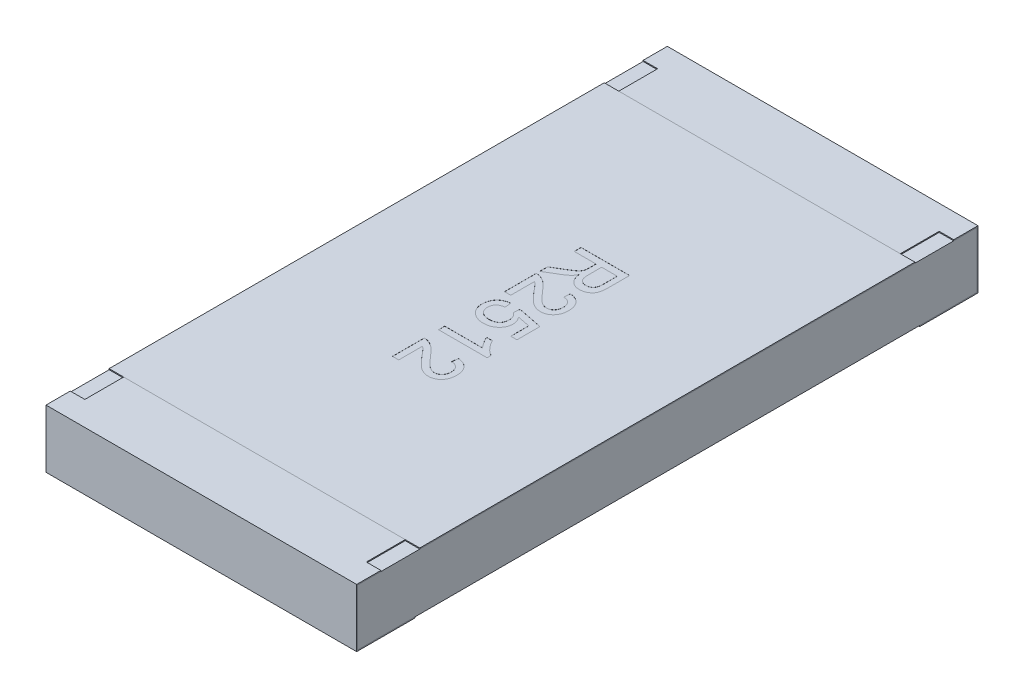
SolidWorks part; units mm, degrees
ref_plane "Front Plane" through (0, 0, 0) normal (0, 0, 1) x (1, 0, 0)
ref_plane "Top Plane" through (0, 0, 0) normal (0, 1, 0) x (1, 0, 0)
ref_plane "Right Plane" through (0, 0, 0) normal (1, 0, 0) x (0, 0, -1)
sketch "Sketch4" plane through (0, 0, 0) normal (1, 0, 0) x (0, 0, -1)
  line L0 (0, 0.1169) -> (0, -0.0721) construction
  line L1 (-3.2, 0) -> (0.3788, 0) construction
  line L2 (-3.2, 0.3) -> (-3.2, -0.3)
  line L3 (-3.2, -0.3) -> (-2.6, -0.3)
  line L4 (-2.55, 0.3) -> (-2.55, 0.29)
  line L5 (-2.55, 0.29) -> (-3.19, 0.29)
  line L6 (-3.19, 0.29) -> (-3.19, -0.29)
  line L7 (-3.19, -0.29) -> (-2.6, -0.29)
  line L8 (-2.6, -0.29) -> (-2.6, -0.3)
  line L9 (-2.55, 0.3) -> (-3.2, 0.3)
  line L10 (2.55, 0.3) -> (3.2, 0.3)
  line L11 (2.6, -0.29) -> (2.6, -0.3)
  line L12 (3.19, -0.29) -> (2.6, -0.29)
  line L13 (3.19, 0.29) -> (3.19, -0.29)
  line L14 (2.55, 0.29) -> (3.19, 0.29)
  line L15 (2.55, 0.3) -> (2.55, 0.29)
  line L16 (3.2, -0.3) -> (2.6, -0.3)
  line L17 (3.2, 0.3) -> (3.2, -0.3)
  dimension "LENGTH" = 3.2
  dimension "HEIGHT" = 0.6
  dimension "END CAP TOP LENGTH" = 0.65
  dimension "END CAP BOTTOM LENGTH" = 0.6
  dimension "D5" = 0.01
  dimension "D6" = 0.01
extrude "Boss-Extrude2" add sketch "Sketch4" along normal mid plane 3.2
sketch "Sketch5" plane through (0, 0, 0) normal (1, 0, 0) x (0, 0, -1)
  line L1 (-3.19, 0.29) -> (3.19, 0.29)
  line L2 (-3.19, 0.29) -> (-3.19, -0.29)
  line L3 (-3.19, -0.29) -> (3.19, -0.29)
  line L4 (3.19, 0.29) -> (3.19, -0.29)
extrude "Boss-Extrude3" add sketch "Sketch5" along normal up to surface and the other way up to surface separate body
sketch "Sketch6" plane through (0, 0.3, 0) normal (0, 1, 0) x (1, 0, 0)
  line L0 (-1.6, 3.2) -> (-1.6, 2.55) construction
  line L1 (-1.6, 2.95) -> (-1.45, 2.95)
  line L2 (-1.6, 2.95) -> (-1.6, 2.55)
  line L3 (-1.6, 2.55) -> (-1.45, 2.55)
  line L4 (-1.45, 2.95) -> (-1.45, 2.55)
  line L5 (1.6, 2.55) -> (-1.6, 2.55) construction
  line L6 (0, 0.0345) -> (0, -0.0345) construction
  line L7 (-0.0325, 0) -> (0.03, 0) construction
  line L8 (1.6, 2.95) -> (1.6, 2.55)
  line L9 (1.6, 2.55) -> (1.45, 2.55)
  line L10 (1.45, 2.95) -> (1.45, 2.55)
  line L11 (1.6, 2.95) -> (1.45, 2.95)
  line L12 (1.6, -2.95) -> (1.45, -2.95)
  line L13 (1.6, -2.95) -> (1.6, -2.55)
  line L14 (1.6, -2.55) -> (1.45, -2.55)
  line L15 (1.45, -2.95) -> (1.45, -2.55)
  line L16 (-1.6, -2.95) -> (-1.45, -2.95)
  line L17 (-1.6, -2.95) -> (-1.6, -2.55)
  line L18 (-1.6, -2.55) -> (-1.45, -2.55)
  line L19 (-1.45, -2.95) -> (-1.45, -2.55)
  dimension "TOP CUT WIDTH" = 0.15
  dimension "TOP CUT LENGTH" = 0.4
extrude "Cut-Extrude1" cut sketch "Sketch6" against normal up to surface (0.01 mm away) up to face at (0, 0.29, 0)
sketch "Sketch7" plane through (0, 0.29, 0) normal (0, 1, 0) x (1, 0, 0)
  line L1 (-1.6, 2.55) -> (1.6, 2.55)
  line L2 (-1.6, 2.55) -> (-1.6, -2.55)
  line L3 (-1.6, -2.55) -> (1.6, -2.55)
  line L4 (1.6, 2.55) -> (1.6, -2.55)
  line L5 (1.45, -2.55) -> (-1.45, -2.55) construction
  line L6 (1.45, 2.55) -> (-1.45, 2.55) construction
  line L7 (-1.6, -3.19) -> (-1.6, 3.19) construction
  line L8 (1.6, 3.19) -> (1.6, -3.19) construction
extrude "Boss-Extrude4" add sketch "Sketch7" along normal up to surface (0.01 mm away) separate body up to face at (0, 0.3, -2.9125)
sketch "Sketch16" plane through (0, 0.3, 0) normal (0, 1, 0) x (1, 0, 0)
  line L0 (-0.25, 1.4279) -> (-0.25, -1.4279) construction
  line L1 (0, 0) -> (-0.25, 0) construction
  text T0 "R2512" font "Arial" height 0.5
  dimension "D1" = 0.25
extrude "TEXT2512" cut sketch "Sketch16" against normal blind 0.001
